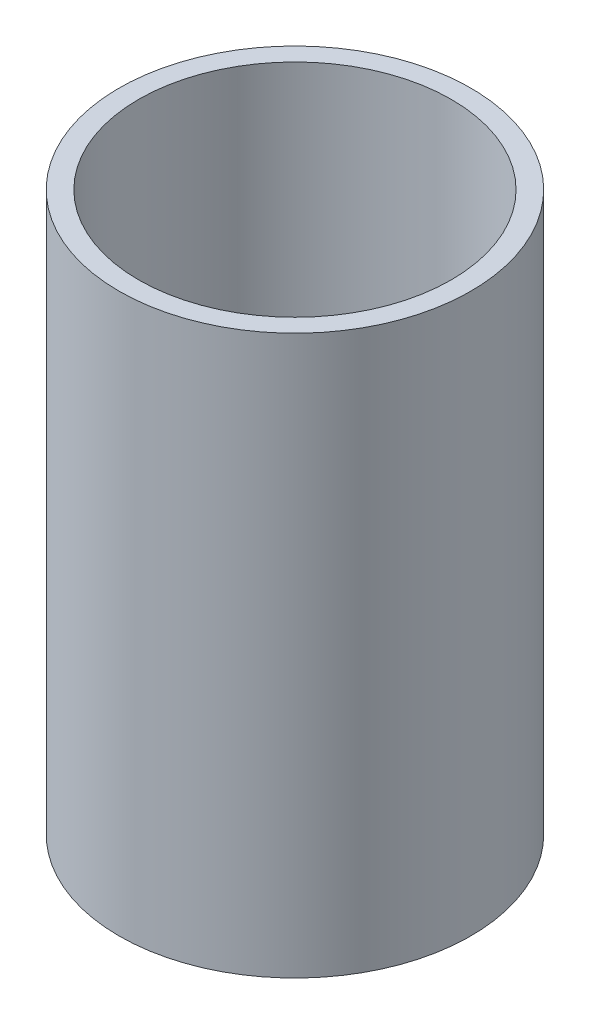
SolidWorks part; units mm, degrees
ref_plane "Plan de face" through (0, 0, 0) normal (0, 0, 1) x (1, 0, 0)
ref_plane "Plan de dessus" through (0, 0, 0) normal (0, 1, 0) x (1, 0, 0)
ref_plane "Plan de droite" through (0, 0, 0) normal (1, 0, 0) x (0, 0, -1)
sketch "Esquisse1" plane through (0, 0, 0) normal (0, 1, 0) x (1, 0, 0)
  circle A0 centre (0, 0) radius 31.5
  circle A1 centre (0, 0) radius 28
  dimension "D1" = 63
  dimension "D2" = 56
extrude "Boss.-Extru.1" add sketch "Esquisse1" along normal blind 100
sketch "Esquisse2" plane through (0, 0, 0) normal (1, 0, 0) x (0, 0, -1)
  line L0 (-31.5, 100) -> (31.5, 0) construction
  line L1 (31.5, 0) -> (31.5, 100) construction
  point P3 (31.5, 18)
  dimension "D1" = 18
